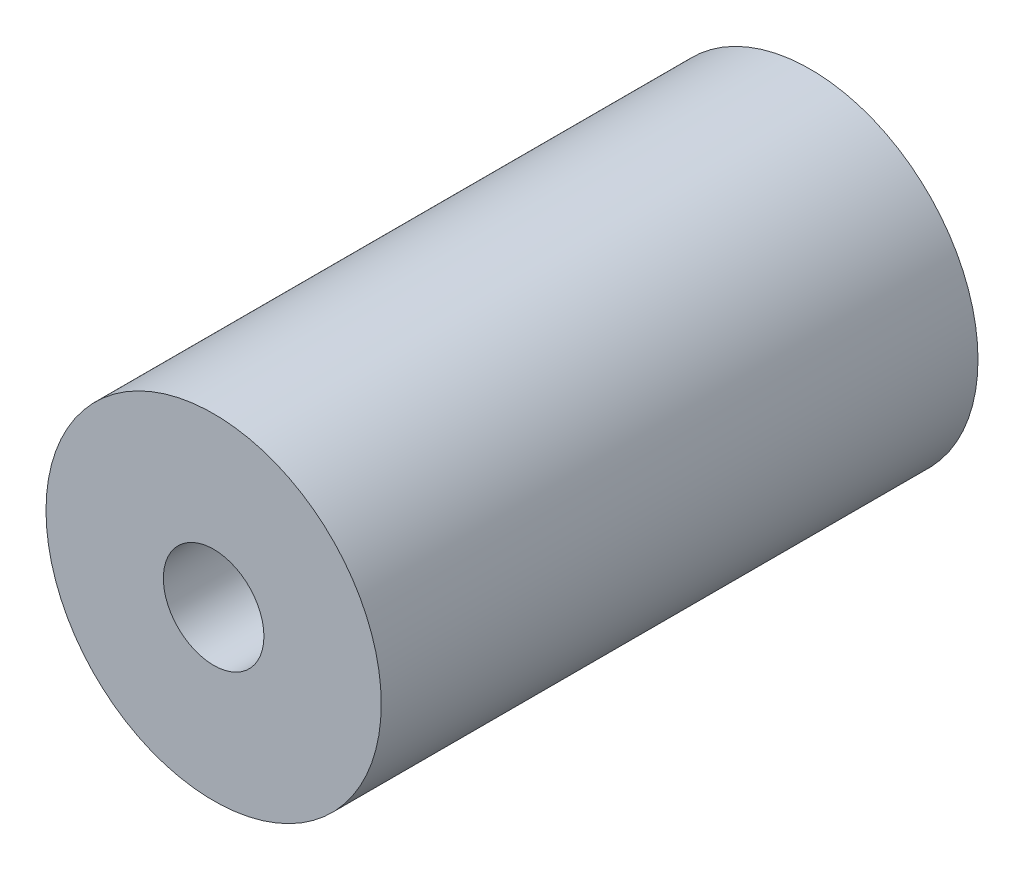
SolidWorks part; units mm, degrees
ref_plane "Front Plane" through (0, 0, 0) normal (0, 0, 1) x (1, 0, 0)
ref_plane "Top Plane" through (0, 0, 0) normal (0, 1, 0) x (1, 0, 0)
ref_plane "Right Plane" through (0, 0, 0) normal (1, 0, 0) x (0, 0, -1)
sketch "Sketch1" plane through (0, 0, 0) normal (0, 0, 1) x (1, 0, 0)
  circle A0 centre (0, 0) radius 5
  dimension "D1" = 10
extrude "Boss-Extrude1" add sketch "Sketch1" along normal blind 17.8
hole_wizard "Ø3.0mm Dowel Hole1" positions "Sketch2" profile "Sketch3" hole size "Ø3.0" standard "ANSI Metric" end condition up to next
sketch "Sketch2" plane through (0, 0, 17.8) normal (0, 0, 1) x (1, 0, 0)
  point P0 (0, 0)
sketch "Sketch3" plane through (0, 0, 17.8) normal (1, 0, 0) x (0, -1, 0)
  line L0 (0, 0) -> (0, 17.8)
  line L1 (0, 17.8) -> (1.5, 17.8)
  line L2 (1.5, 17.8) -> (1.5, 0)
  line L5 (1.5, 0) -> (0, 0)
  line L11 (0, -6.35) -> (0, 107.95) construction
  dimension "Thru Hole Dia." = 3
  dimension "Thru Hole Depth" = 17.8
